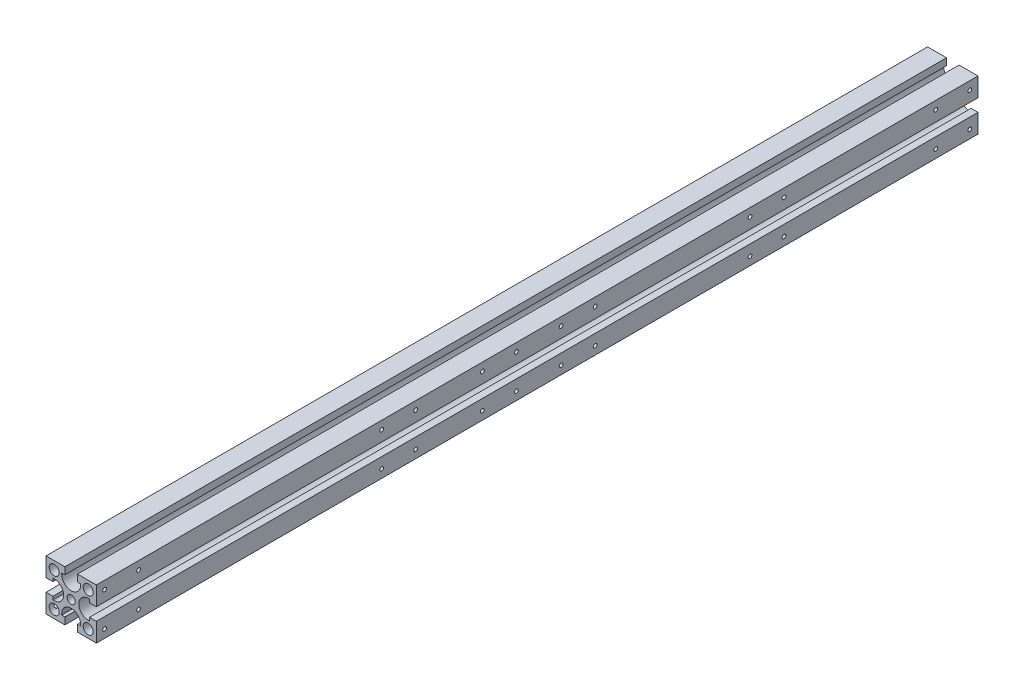
SolidWorks part; units mm, degrees
ref_plane "前基準面" through (0, 0, 0) normal (0, 0, 1) x (1, 0, 0)
ref_plane "上基準面" through (0, 0, 0) normal (0, 1, 0) x (1, 0, 0)
ref_plane "右基準面" through (0, 0, 0) normal (1, 0, 0) x (0, 0, -1)
sketch "草圖1" plane through (0, 0, 0) normal (0, 0, 1) x (1, 0, 0)
  line L0 (0, 20) -> (0, -20) construction
  line L1 (-20, -20) -> (20, -20)
  line L2 (-20, -20) -> (-20, 20)
  line L3 (-20, 20) -> (20, 20)
  line L4 (20, -20) -> (20, 20)
  dimension "D1" = 40
  dimension "D2" = 40
extrude "伸長1" add sketch "草圖1" along normal blind 700
sketch "草圖2" plane through (0, 0, 0) normal (0, 0, -1) x (-1, 0, 0)
  line L0 (-20, 20) -> (20, 20) construction
  line L4 (5, 14.5) -> (7.5, 14.5)
  line L5 (14.5, -5) -> (14.5, -7.5)
  line L6 (-5, 14.5) -> (-5, 20)
  line L7 (-5, 20) -> (5, 20)
  line L8 (5, 14.5) -> (5, 20)
  line L9 (14.5, 5) -> (20, 5)
  line L10 (-7.5, 13.5) -> (-7.5, 14.5)
  line L11 (-7.5, 14.5) -> (-5, 14.5)
  line L12 (7.5, 13.5) -> (7.5, 14.5)
  line L13 (20, 5) -> (20, -5)
  line L14 (14.5, -5) -> (20, -5)
  line L15 (13.5, 7.5) -> (14.5, 7.5)
  line L16 (14.5, 7.5) -> (14.5, 5)
  line L17 (13.5, -7.5) -> (14.5, -7.5)
  line L18 (-5, -14.5) -> (-7.5, -14.5)
  line L19 (5, -14.5) -> (5, -20)
  line L20 (5, -20) -> (-5, -20)
  line L21 (-5, -14.5) -> (-5, -20)
  line L22 (7.5, -13.5) -> (7.5, -14.5)
  line L23 (7.5, -14.5) -> (5, -14.5)
  line L24 (-7.5, -13.5) -> (-7.5, -14.5)
  line L25 (-14.5, 5) -> (-14.5, 7.5)
  line L26 (-14.5, -5) -> (-20, -5)
  line L27 (-20, -5) -> (-20, 5)
  line L28 (-14.5, 5) -> (-20, 5)
  line L29 (-13.5, -7.5) -> (-14.5, -7.5)
  line L30 (-14.5, -7.5) -> (-14.5, -5)
  line L31 (-13.5, 7.5) -> (-14.5, 7.5)
  line L32 (0, -20) -> (0, 0) construction
  line L33 (20, -20) -> (-20, -20) construction
  line L34 (0, 0) -> (-20, 0) construction
  line L35 (-20, -20) -> (-20, 20) construction
  line L36 (20, 20) -> (20, -20) construction
  circle A0 centre (0, 0) radius 3.25
  circle A1 centre (-13.5, 13.5) radius 4
  circle A2 centre (13.5, 13.5) radius 4
  circle A3 centre (-13.5, -13.5) radius 4
  circle A4 centre (13.5, -13.5) radius 4
  arc A5 (-7.5, 13.5) -> (7.5, 13.5) centre (0, 13.5) ccw
  arc A6 (13.5, 7.5) -> (13.5, -7.5) centre (13.5, 0) ccw
  arc A7 (7.5, -13.5) -> (-7.5, -13.5) centre (0, -13.5) ccw
  arc A8 (-13.5, -7.5) -> (-13.5, 7.5) centre (-13.5, 0) ccw
  dimension "D1" = 6.5
  dimension "D2" = 8
  dimension "D5" = 15
  dimension "D12" = 5.5
  dimension "D3" = 27
  dimension "D4" = 27
  dimension "D6" = 10
extrude "除料-伸長1" cut sketch "草圖2" against normal through all
hole_wizard "M3x0.5 螺紋孔1" positions "草圖6" profile "草圖5" tap size "M3x0.5" standard "JIS"
sketch "草圖6" plane through (-20, 0, 0) normal (-1, 0, 0) x (0, 0, 1)
  line L27 (700, 13.5) -> (0, 13.5) construction
  line L28 (700, 20) -> (700, 5) construction
  line L29 (0, 20) -> (0, 5) construction
  line L32 (700, 0) -> (0, 0) construction
  line L35 (700, 20) -> (0, 20) construction
  line L36 (700, -13.5) -> (0, -13.5) construction
  point P113 (6.5, 13.5)
  point P115 (33.5, 13.5)
  point P117 (176.5, 13.5)
  point P119 (203.5, 13.5)
  point P137 (203.5, -13.5)
  point P138 (176.5, -13.5)
  point P139 (33.5, -13.5)
  point P140 (6.5, -13.5)
  point P145 (695, 15)
  point P147 (520, 15)
  point P156 (520, -15)
  point P157 (695, -15)
  dimension "D1" = 6.5
  dimension "D2" = 6.5
  dimension "D3" = 27
  dimension "D4" = 170
  dimension "D5" = 27
  dimension "D6" = 5
  dimension "D7" = 5
  dimension "D8" = 175
  dimension "D9" = 5
sketch "草圖5" plane through (-20, 13.5, 6.5) normal (0, 1, 0) x (0, 0, 1)
  line L0 (0, 0) -> (0, 8.2511)
  line L1 (0, 8.2511) -> (1.25, 7.5)
  line L2 (1.25, 7.5) -> (1.25, 6)
  line L3 (1.25, 6) -> (1.5, 6)
  line L4 (1.5, 6) -> (1.5, 0)
  line L5 (1.5, 0) -> (0, 0)
  line L10 (0, 8.2511) -> (-1.25, 7.5) construction
  line L11 (0, -6.35) -> (0, 107.95) construction
  dimension "螺孔鑽直徑" = 2.5
  dimension "螺孔鑽深度" = 7.5
  dimension "螺紋主直徑" = 3
  dimension "螺紋深度" = 6
  dimension "導頭角度" = 118
hole_wizard "M3x0.5 螺紋孔2" positions "草圖8" profile "草圖7" tap size "M3x0.5" standard "JIS"
sketch "草圖8" plane through (20, 0, 0) normal (1, 0, 0) x (0, 0, -1)
  line L10 (-700, -13.5) -> (0, -13.5) construction
  line L11 (-700, -20) -> (-700, -5) construction
  line L12 (0, -20) -> (0, -5) construction
  line L15 (-700, 0) -> (0, 0) construction
  line L19 (-700, -20) -> (0, -20) construction
  line L37 (-700, 13.5) -> (0, 13.5) construction
  point P100 (-693.5, -13.5)
  point P102 (-666.5, -13.5)
  point P110 (-446.5, -13.5)
  point P112 (-473.5, -13.5)
  point P127 (-304, -13.5)
  point P129 (-331, -13.5)
  point P132 (-154, -13.5)
  point P134 (-181, -13.5)
  point P137 (-6.5, -13.5)
  point P139 (-33.5, -13.5)
  point P142 (-393.5, -13.5)
  point P145 (-366.5, -13.5)
  point P150 (-366.5, 13.5)
  point P151 (-393.5, 13.5)
  point P152 (-33.5, 13.5)
  point P153 (-6.5, 13.5)
  point P154 (-181, 13.5)
  point P155 (-154, 13.5)
  point P156 (-331, 13.5)
  point P157 (-304, 13.5)
  point P158 (-473.5, 13.5)
  point P159 (-446.5, 13.5)
  point P160 (-666.5, 13.5)
  point P161 (-693.5, 13.5)
  dimension "D1" = 6.5
  dimension "D2" = 6.5
  dimension "D3" = 27
  dimension "D4" = 220
  dimension "D5" = 27
  dimension "D6" = 142.5
  dimension "D7" = 27
  dimension "D8" = 150
  dimension "D9" = 27
  dimension "D10" = 6.5
  dimension "D11" = 27
  dimension "D12" = 360
  dimension "D13" = 27
sketch "草圖7" plane through (20, -13.5, 693.5) normal (0, 1, 0) x (0, 0, -1)
  line L0 (0, 0) -> (0, 8.2511)
  line L1 (0, 8.2511) -> (1.25, 7.5)
  line L2 (1.25, 7.5) -> (1.25, 6)
  line L3 (1.25, 6) -> (1.5, 6)
  line L4 (1.5, 6) -> (1.5, 0)
  line L5 (1.5, 0) -> (0, 0)
  line L10 (0, 8.2511) -> (-1.25, 7.5) construction
  line L11 (0, -6.35) -> (0, 107.95) construction
  dimension "螺孔鑽直徑" = 2.5
  dimension "螺孔鑽深度" = 7.5
  dimension "螺紋主直徑" = 3
  dimension "螺紋深度" = 6
  dimension "導頭角度" = 118
